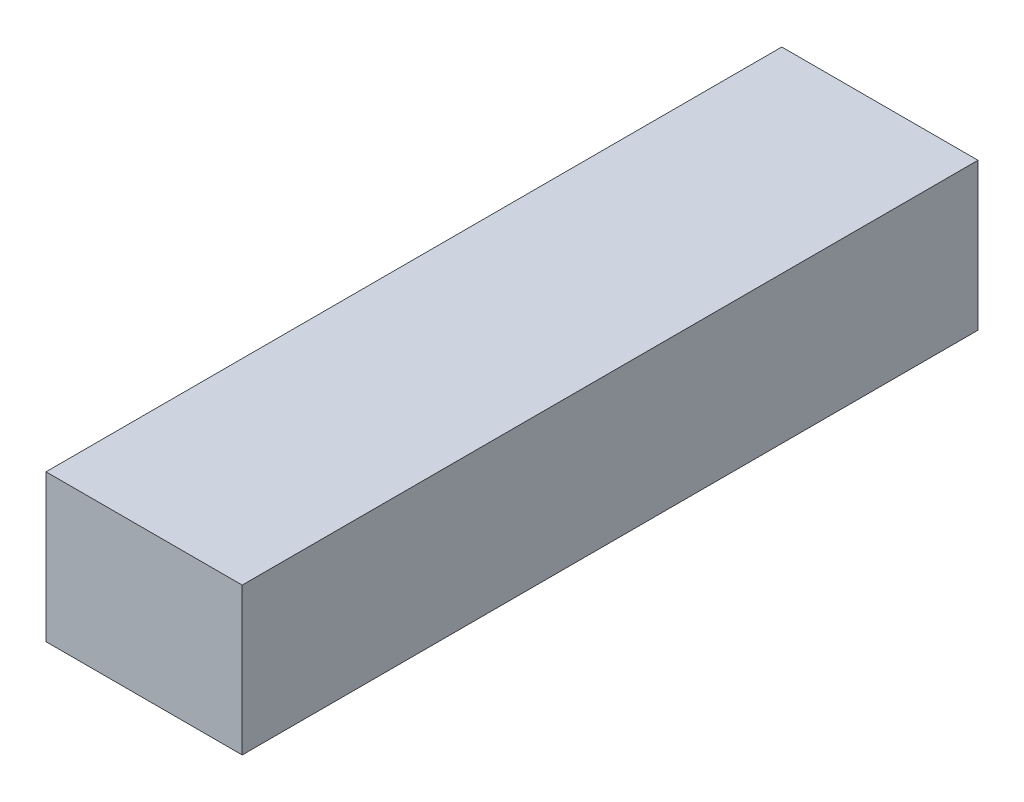
SolidWorks part; units mm, degrees
ref_plane "Спереди" through (0, 0, 0) normal (0, 0, 1) x (1, 0, 0)
ref_plane "Сверху" through (0, 0, 0) normal (0, 1, 0) x (1, 0, 0)
ref_plane "Справа" through (0, 0, 0) normal (1, 0, 0) x (0, 0, -1)
sketch "Эскиз1" plane through (0, 0, 0) normal (0, 1, 0) x (1, 0, 0)
  line L1 (-20, 75) -> (20, 75)
  line L2 (-20, 75) -> (-20, -75)
  line L3 (-20, -75) -> (20, -75)
  line L4 (20, 75) -> (20, -75)
  line L5 (-20, 75) -> (20, -75) construction
  line L6 (-20, -75) -> (20, 75) construction
  point P0 (0, 0)
extrude "Бобышка-Вытянуть1" add sketch "Эскиз1" along normal blind 30
